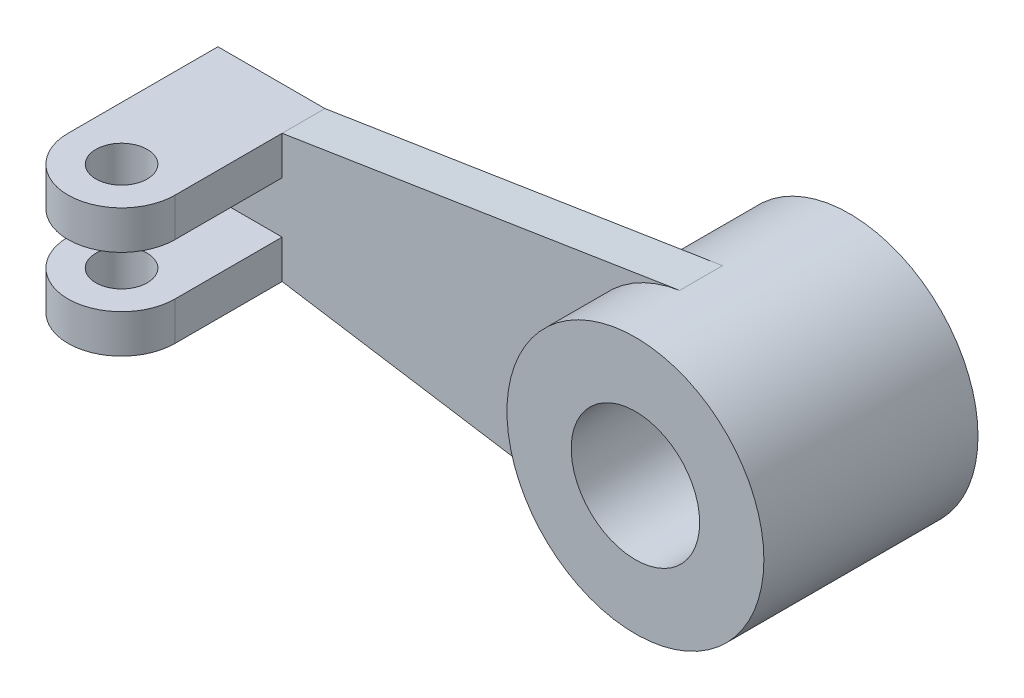
SolidWorks part; units mm, degrees
ref_plane "Front Plane" through (0, 0, 0) normal (0, 0, 1) x (1, 0, 0)
ref_plane "Top Plane" through (0, 0, 0) normal (0, 1, 0) x (1, 0, 0)
ref_plane "Right Plane" through (0, 0, 0) normal (1, 0, 0) x (0, 0, -1)
sketch "Sketch1" plane through (0, 0, 0) normal (0, 0, 1) x (1, 0, 0)
  circle A0 centre (0, 0) radius 30
extrude "Boss-Extrude1" add sketch "Sketch1" along normal mid plane 50
sketch "Sketch2" plane through (0, 0, 25) normal (0, 0, 1) x (1, 0, 0)
  circle A0 centre (0, 0) radius 15
extrude "Cut-Extrude1" cut sketch "Sketch2" against normal blind 50
sketch "Sketch6" plane through (0, 0, 0) normal (0, 0, 1) x (1, 0, 0)
  line L0 (-4.6717, 29.634) -> (-97.5, 15)
  line L1 (-97.5, 15) -> (-122.5, 15)
  line L2 (-122.5, 15) -> (-122.5, -15)
  line L3 (-122.5, 0) -> (0, 0) construction
  line L4 (-4.6717, -29.634) -> (-97.5, -15)
  line L5 (-97.5, -15) -> (-122.5, -15)
  circle A0 centre (0, 0) radius 30 construction
  arc A1 (-4.6717, 29.634) -> (-4.6717, -29.634) centre (0, 0) ccw
  dimension "D1" = 25
  dimension "D2" = 30
  dimension "D3" = 122.5
extrude "Boss-Extrude3" add sketch "Sketch6" along normal blind 10 contours L1 L2 L5 L4 A1 L0
sketch "Sketch8" plane through (0, -15, 0) normal (0, -1, 0) x (1, 0, 0)
  line L0 (-122.5, 10) -> (-122.5, 35)
  line L1 (-97.5, 10) -> (-97.5, 35)
  line L2 (-122.5, 10) -> (-97.5, 10)
  arc A0 (-122.5, 35) -> (-97.5, 35) centre (-110, 35) cw
  circle A1 centre (-110, 35) radius 6
  dimension "D1" = 12
  dimension "D2" = 25
extrude "Boss-Extrude4" add sketch "Sketch8" against normal blind 9
mirror "Mirror1" about plane through (0, 0, 0) normal (0, 1, 0) of "Boss-Extrude4"
